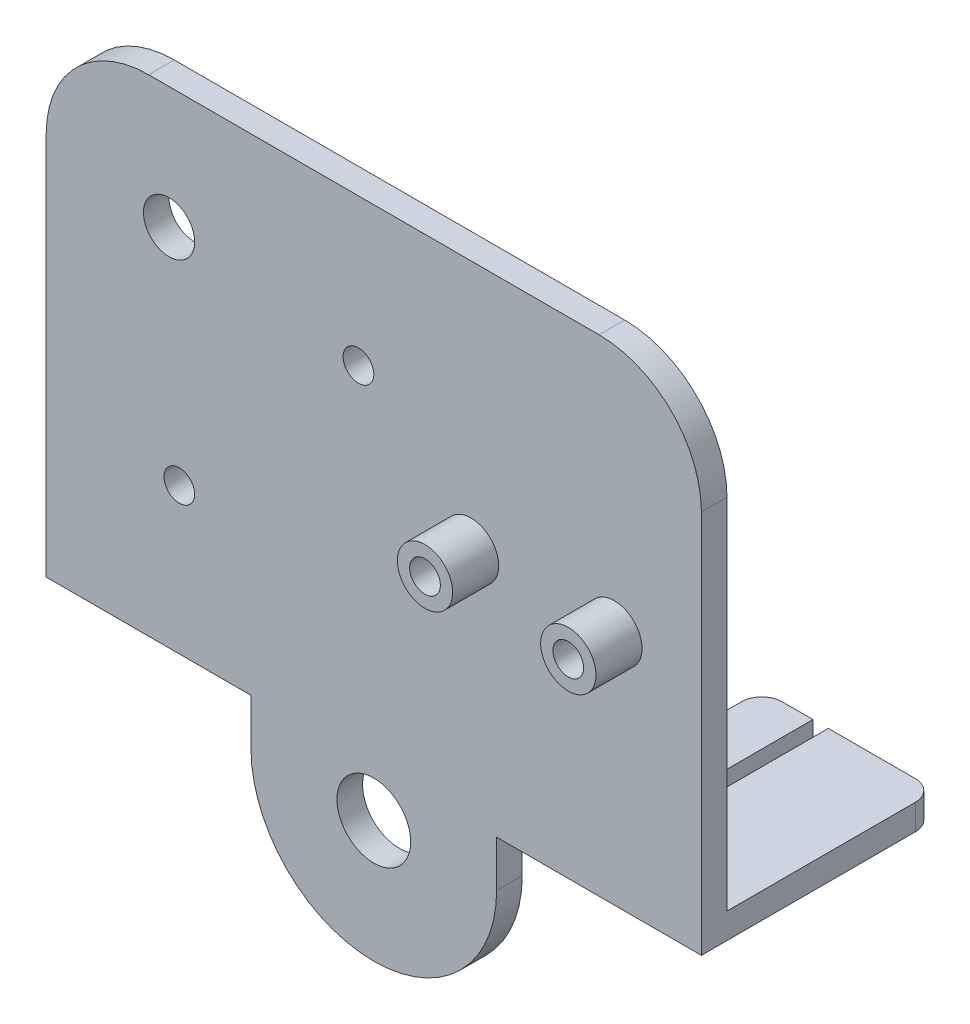
SolidWorks part; units mm, degrees
ref_plane "Front Plane" through (0, 0, 0) normal (0, 0, 1) x (1, 0, 0)
ref_plane "Top Plane" through (0, 0, 0) normal (0, 1, 0) x (1, 0, 0)
ref_plane "Right Plane" through (0, 0, 0) normal (1, 0, 0) x (0, 0, -1)
ref_plane "Plane1" through (0, 0, 0) normal (0, 0, -1) x (-1, 0, 0)
sketch "Sketch1" plane through (0, 0, 0) normal (0, 0, -1) x (-1, 0, 0)
  line L0 (12, -20) -> (12, 32)
  line L1 (12, 32) -> (-12, 32)
  line L2 (-12, 32) -> (-12, -20)
  arc A0 (-12, -20) -> (12, -20) centre (0, -20) ccw
extrude "Boss-Extrude1" add sketch "Sketch1" against normal blind 2.5
sketch "Sketch2" plane through (-12, 0, 0) normal (-1, 0, 0) x (0, 0, 1)
  line L0 (0, -15.5) -> (0, 32)
  line L1 (0, 32) -> (2.5, 32)
  line L2 (2.5, 32) -> (2.5, -15.5)
  line L3 (2.5, -15.5) -> (0, -15.5)
extrude "Boss-Extrude2" add sketch "Sketch2" along normal blind 20
sketch "Sketch3" plane through (12, 0, 0) normal (1, 0, 0) x (0, 0, -1)
  line L0 (0, -15.5) -> (-2.5, -15.5)
  line L1 (-2.5, -15.5) -> (-2.5, 32)
  line L2 (-2.5, 32) -> (0, 32)
  line L3 (0, 32) -> (0, -15.5)
extrude "Boss-Extrude3" add sketch "Sketch3" along normal blind 20
sketch "Sketch4" plane through (0, 0, 0) normal (0, 0, -1) x (-1, 0, 0)
  line L0 (-32, -13) -> (-15, -13)
  line L1 (-15, -13) -> (-15, -15.5)
  line L2 (-15, -15.5) -> (-32, -15.5)
  line L3 (-32, -15.5) -> (-32, -13)
extrude "Boss-Extrude4" add sketch "Sketch4" along normal blind 20.4
sketch "Sketch5" plane through (0, -15.5, 0) normal (0, -1, 0) x (1, 0, 0)
  line L0 (21.5, -20.4) -> (21.5, -9.4)
  line L1 (21.5, -9.4) -> (20, -9.4)
  line L2 (20, -9.4) -> (20, -20.4)
  line L3 (20, -20.4) -> (21.5, -20.4)
extrude "Cut-Extrude1" cut sketch "Sketch5" against normal through all
sketch "Sketch6" plane through (0, 0, 0) normal (0, 0, -1) x (-1, 0, 0)
  line L0 (15, -13) -> (32, -13)
  line L1 (32, -13) -> (32, -15.5)
  line L2 (32, -15.5) -> (15, -15.5)
  line L3 (15, -15.5) -> (15, -13)
extrude "Boss-Extrude5" add sketch "Sketch6" along normal blind 20.4
sketch "Sketch7" plane through (0, -15.5, 0) normal (0, -1, 0) x (1, 0, 0)
  line L0 (-20, -20.4) -> (-20, -9.4)
  line L1 (-20, -9.4) -> (-21.5, -9.4)
  line L2 (-21.5, -9.4) -> (-21.5, -20.4)
  line L3 (-21.5, -20.4) -> (-20, -20.4)
extrude "Cut-Extrude2" cut sketch "Sketch7" against normal through all
ref_plane "Plane2" through (0, 7.55, 0) normal (0, 1, 0) x (1, 0, 0)
sketch "Sketch8" plane through (0, 7.55, 0) normal (0, 1, 0) x (1, 0, 0)
  line L0 (12.2, -2.5) -> (9.5, -2.5)
  line L1 (9.5, -2.5) -> (9.5, -7)
  line L2 (9.5, -7) -> (12.2, -7)
  line L3 (12.2, -7) -> (12.2, -2.5)
  line L4 (9.5, -2.5) -> (9.5, -7) construction
revolve "Revolve1" add sketch "Sketch8" angle 360 about L4
sketch "Sketch9" plane through (0, 7.55, 0) normal (0, 1, 0) x (1, 0, 0)
  line L0 (26.2, -2.5) -> (23.5, -2.5)
  line L1 (23.5, -2.5) -> (23.5, -7)
  line L2 (23.5, -7) -> (26.2, -7)
  line L3 (26.2, -7) -> (26.2, -2.5)
  line L4 (23.5, -2.5) -> (23.5, -7) construction
revolve "Revolve2" add sketch "Sketch9" angle 360 about L4
ref_plane "Plane3" through (0, -1.25, 0) normal (0, -1, 0) x (1, 0, 0)
sketch "Sketch10" plane through (0, -1.25, 0) normal (0, -1, 0) x (1, 0, 0)
  line L0 (-17, 0) -> (-19, 0)
  line L1 (-19, 0) -> (-19, -1.5)
  line L2 (-19, -1.5) -> (-17, -1.5)
  line L3 (-17, -1.5) -> (-17, 0)
  line L4 (-19, 0) -> (-19, -1.5) construction
revolve "Revolve3" add sketch "Sketch10" angle 360 about L4
ref_plane "Plane4" through (0, 17.65, 0) normal (0, -1, 0) x (1, 0, 0)
sketch "Sketch11" plane through (0, 17.65, 0) normal (0, -1, 0) x (1, 0, 0)
  line L0 (0.5, 0) -> (-1.5, 0)
  line L1 (-1.5, 0) -> (-1.5, -1.5)
  line L2 (-1.5, -1.5) -> (0.5, -1.5)
  line L3 (0.5, -1.5) -> (0.5, 0)
  line L4 (-1.5, 0) -> (-1.5, -1.5) construction
revolve "Revolve4" add sketch "Sketch11" angle 360 about L4
fillet "Fillet1" radius 2 4 edges at (32, -14.25, -20.4) (-15, -14.25, -20.4) (15, -14.25, -20.4) (-32, -14.25, -20.4)
fillet "Fillet2" radius 10 2 edges at (32, 32, 1.25) (-32, 32, 1.25)
sketch "Sketch12" plane through (0, 0, 2.5) normal (0, 0, 1) x (1, 0, 0)
  line L0 (0, -20.1) -> (0, 20.1) construction
  line L1 (0, 20.1) -> (-20, 20.1) construction
  line L2 (0, 0) -> (-40.4414, 0) construction
sketch "Sketch13" plane through (0, 0, 2.5) normal (0, 0, 1) x (1, 0, 0)
  line L0 (-19, -1.25) -> (-1.5, -1.25) construction
  line L1 (-1.5, -1.25) -> (-1.5, 17.65) construction
  line L2 (-1.5, 17.65) -> (-19, 17.65) construction
  line L3 (-19, 17.65) -> (-19, -1.25) construction
  line L4 (-1.5, 17.65) -> (0, 17.65) construction
  line L5 (0, -20.1) -> (0, 20.1) construction
  line L6 (-19, -1.25) -> (-32, -1.25) construction
  line L7 (-32, -15.5) -> (-32, 22) construction
  line L8 (-19, -1.25) -> (-19, -15.5) construction
  line L9 (-32, -15.5) -> (-12, -15.5) construction
  line L10 (0, 20.1) -> (-20, 20.1) construction
  circle A0 centre (0, -20.1) radius 3.6
  circle A1 centre (-20, 20.1) radius 2.5
  circle A2 centre (-1.5, 17.65) radius 1.5
  circle A3 centre (-19, -1.25) radius 1.5
  circle A4 centre (9.5, 7.55) radius 1.5
  circle A5 centre (23.5, 7.55) radius 1.5
  dimension "D1" = 7.2
  dimension "D2" = 5
  dimension "D3" = 3
  dimension "D4" = 3
  dimension "D9" = 3
  dimension "D10" = 3
  dimension "D5" = 1.5
  dimension "D6" = 13
  dimension "D7" = 14.25
  dimension "D8" = 2.45
extrude "Cut-Extrude3" cut sketch "Sketch13" against normal through all both and the other way through all
